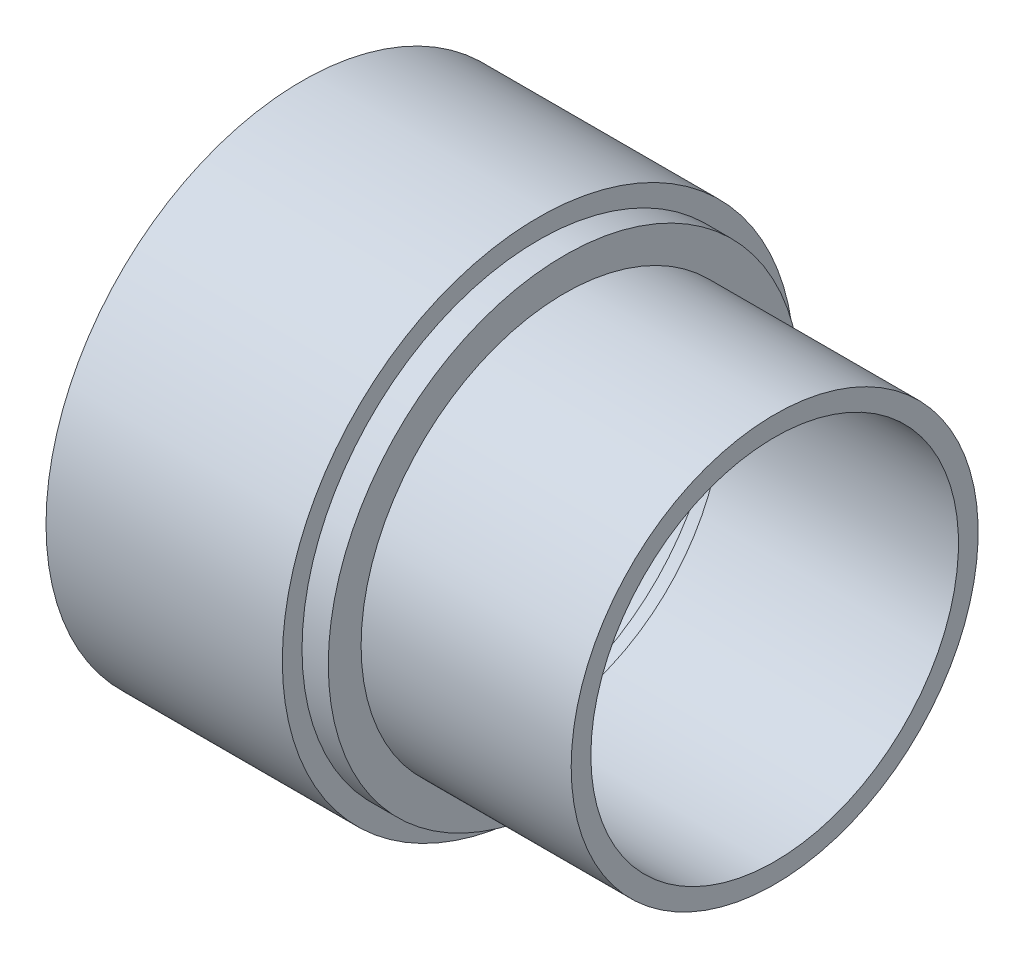
SolidWorks part; units mm, degrees
ref_plane "Front" through (0, 0, 0) normal (0, 0, 1) x (1, 0, 0)
ref_plane "Top" through (0, 0, 0) normal (0, 1, 0) x (1, 0, 0)
ref_plane "Right" through (0, 0, 0) normal (1, 0, 0) x (0, 0, -1)
sketch "Sketch1" plane through (0, 0, 0) normal (0, 0, 1) x (1, 0, 0)
  line L0 (0, 49.2125) -> (0, 0) construction
  line L1 (6.35, 57.15) -> (-6.35, 57.15)
  line L2 (6.35, 57.15) -> (6.35, 49.2125)
  line L3 (6.35, 49.2125) -> (-6.35, 49.2125)
  line L4 (-6.35, 57.15) -> (-6.35, 49.2125)
  line L5 (0, 0) -> (47.7024, 0) construction
  dimension "D1" = 12.7
  dimension "D2" = 98.425
  dimension "D3" = 114.3
revolve "Revolve1" add sketch "Sketch1" angle 360 about L5
sketch "Sketch2" plane through (0, 0, 0) normal (0, 0, 1) x (1, 0, 0)
  line L0 (6.35, 57.15) -> (-6.35, 57.15) construction
  line L1 (0, 57.15) -> (-57.15, 57.15)
  line L2 (0, 57.15) -> (0, 61.9125)
  line L3 (0, 61.9125) -> (-57.15, 61.9125)
  line L4 (-57.15, 57.15) -> (-57.15, 61.9125)
  line L5 (6.35, 49.2125) -> (-6.35, 49.2125) construction
  line L6 (0, 49.2125) -> (57.15, 49.2125)
  line L7 (0, 49.2125) -> (0, 44.45)
  line L8 (0, 44.45) -> (57.15, 44.45)
  line L9 (57.15, 49.2125) -> (57.15, 44.45)
  line L10 (0, 0) -> (97.2197, 0) construction
  line L11 (-6.35, 57.15) -> (-6.35, -57.15) construction
  line L12 (6.35, -57.15) -> (6.35, 57.15) construction
  dimension "D1" = 4.7625
  dimension "D2" = 4.7625
  dimension "D3" = 114.3
  dimension "D4" = 50.8
  dimension "D5" = 50.8
revolve "Revolve2" add sketch "Sketch2" angle 360 about L10
